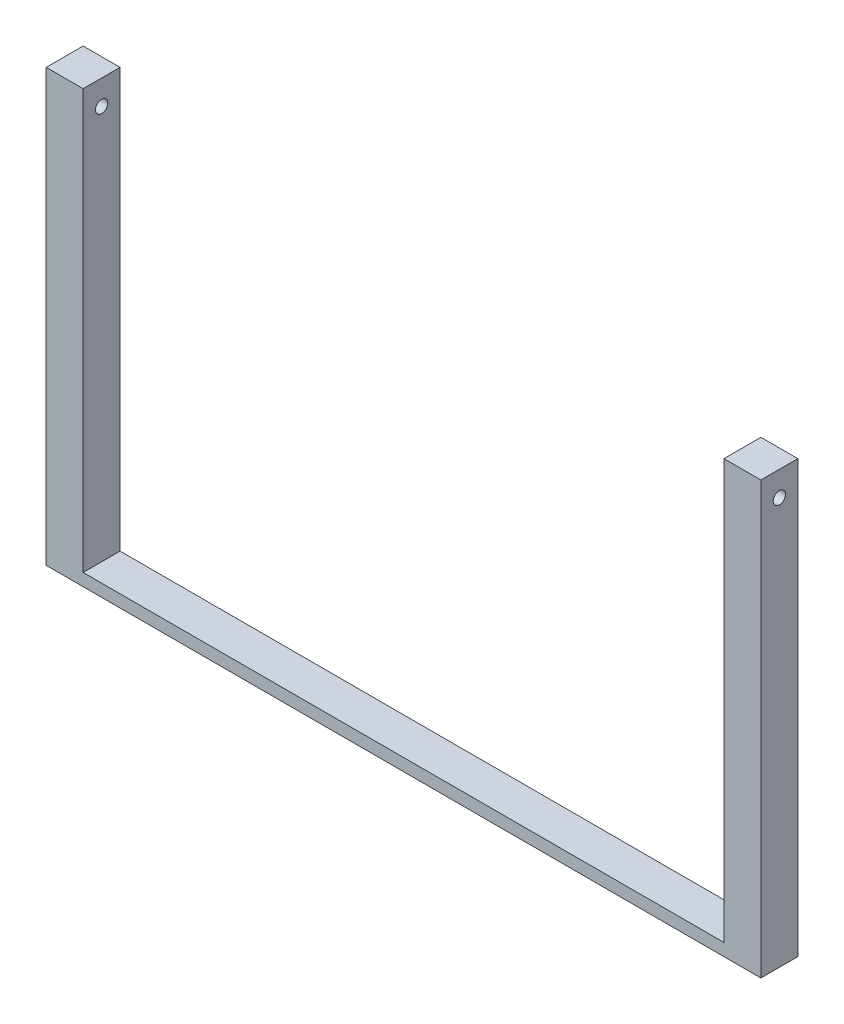
SolidWorks part; units mm, degrees
material "Massless"
ref_plane "Front Plane" through (0, 0, 0) normal (0, 0, 1) x (1, 0, 0)
ref_plane "Top Plane" through (0, 0, 0) normal (0, 1, 0) x (1, 0, 0)
ref_plane "Right Plane" through (0, 0, 0) normal (1, 0, 0) x (0, 0, -1)
sketch "Sketch2" plane through (0, 0, 0) normal (0, 1, 0) x (1, 0, 0)
  line L1 (-368.3, 19.05) -> (368.3, 19.05)
  line L2 (-368.3, 19.05) -> (-368.3, -19.05)
  line L3 (-368.3, -19.05) -> (368.3, -19.05)
  line L4 (368.3, 19.05) -> (368.3, -19.05)
  line L5 (-368.3, 19.05) -> (368.3, -19.05) construction
  line L6 (-368.3, -19.05) -> (368.3, 19.05) construction
  point P0 (0, 0)
  dimension "D1" = 736.6
  dimension "D2" = 38.1
extrude "Boss-Extrude1" add sketch "Sketch2" along normal blind 12.7
sketch "Sketch3" plane through (0, 12.7, 0) normal (0, 1, 0) x (1, 0, 0)
  line L1 (-330.2, -19.05) -> (-368.3, -19.05)
  line L2 (-330.2, -19.05) -> (-330.2, 19.05)
  line L3 (-330.2, 19.05) -> (-368.3, 19.05)
  line L4 (-368.3, -19.05) -> (-368.3, 19.05)
  line L5 (-330.2, -19.05) -> (-368.3, 19.05) construction
  line L6 (-330.2, 19.05) -> (-368.3, -19.05) construction
  line L7 (330.2, -19.05) -> (368.3, -19.05)
  line L8 (330.2, -19.05) -> (330.2, 19.05)
  line L9 (330.2, 19.05) -> (368.3, 19.05)
  line L10 (368.3, -19.05) -> (368.3, 19.05)
  line L11 (330.2, -19.05) -> (368.3, 19.05) construction
  line L12 (330.2, 19.05) -> (368.3, -19.05) construction
  point P0 (-349.25, 0)
  point P6 (349.25, 0)
  dimension "D1" = 38.1
  dimension "D2" = 38.1
extrude "Boss-Extrude2" add sketch "Sketch3" along normal blind 431.8
sketch "Sketch4" plane through (368.3, 0, 0) normal (1, 0, 0) x (0, 0, -1)
  line L0 (-19.05, 444.5) -> (19.05, 444.5) construction
  circle A0 centre (0, 419.1) radius 6.35
  dimension "D1" = 25.4
  dimension "D2" = 12.7
extrude "Cut-Extrude1" cut sketch "Sketch4" against normal through all
